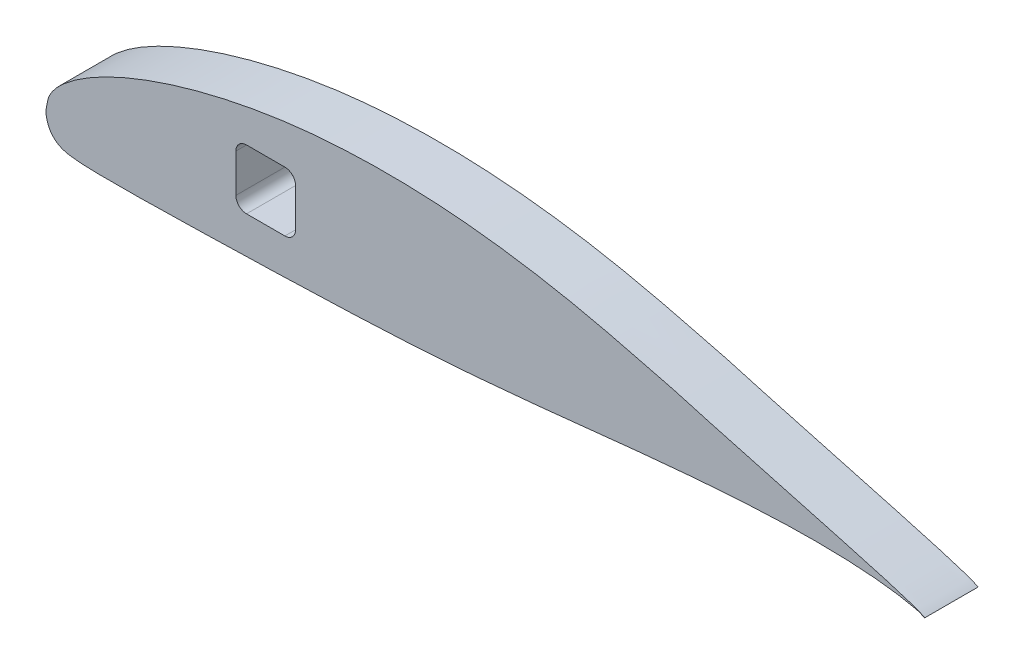
SolidWorks part; units mm, degrees
material "Wing Foam"
ref_plane "Front Plane" through (0, 0, 0) normal (0, 0, 1) x (1, 0, 0)
ref_plane "Top Plane" through (0, 0, 0) normal (0, 1, 0) x (1, 0, 0)
ref_plane "Right Plane" through (0, 0, 0) normal (1, 0, 0) x (0, 0, -1)
curve "Curve1"
  spline degree 3 poles (25.2073, 0.0831, 0) (25.4867, -0.0413, 0) (25.2065, 0.1018, 0) (25.0451, 0.1488, 0) (24.7905, 0.2354, 0) (24.512, 0.3191, 0) (24.1862, 0.415, 0) (23.8224, 0.5184, 0) (23.4192, 0.6311, 0) (22.9787, 0.7524, 0) (22.5024, 0.8828, 0) (21.992, 1.0218, 0) (21.4492, 1.1695, 0) (20.8759, 1.3256, 0) (20.2741, 1.4891, 0) (19.6466, 1.6619, 0) (18.9917, 1.8333, 0) (18.325, 2.0421, 0) (17.625, 2.2014, 0) (16.918, 2.3933, 0) (16.1932, 2.5703, 0) (15.4566, 2.7375, 0) (14.7104, 2.8879, 0) (13.9573, 3.0202, 0) (13.2001, 3.1321, 0) (12.4415, 3.2228, 0) (11.684, 3.2913, 0) (10.9305, 3.3367, 0) (10.1835, 3.3587, 0) (9.4457, 3.3585, 0) (8.7197, 3.336, 0) (8.0081, 3.2917, 0) (7.3132, 3.2267, 0) (6.6377, 3.1395, 0) (5.9841, 3.0331, 0) (5.3544, 2.9102, 0) (4.7508, 2.7729, 0) (4.1756, 2.6228, 0) (3.6307, 2.4616, 0) (3.118, 2.2911, 0) (2.6394, 2.1129, 0) (2.1964, 1.9285, 0) (1.7907, 1.7399, 0) (1.4236, 1.5487, 0) (1.0964, 1.3566, 0) (0.8101, 1.1655, 0) (0.5655, 0.9766, 0) (0.3618, 0.7902, 0) (0.2027, 0.6023, 0) (0.0715, 0.3961, 0) (0.0291, 0.1867, 0) (-0.0105, -0.0161, 0) (0.0146, -0.202, 0) (0.0835, -0.3893, 0) (0.1957, -0.5546, 0) (0.3573, -0.6861, 0) (0.5679, -0.7631, 0) (0.8154, -0.8005, 0) (1.1017, -0.8208, 0) (1.4284, -0.8311, 0) (1.795, -0.8378, 0) (2.2003, -0.8263, 0) (2.6429, -0.8333, 0) (3.1212, -0.8225, 0) (3.6335, -0.8137, 0) (4.1782, -0.8014, 0) (4.7531, -0.7878, 0) (5.3564, -0.7722, 0) (5.9859, -0.755, 0) (6.6394, -0.7358, 0) (7.3145, -0.7145, 0) (8.009, -0.6907, 0) (8.7203, -0.6638, 0) (9.446, -0.6335, 0) (10.1835, -0.5982, 0) (10.9302, -0.5555, 0) (11.6834, -0.5048, 0) (12.4406, -0.4465, 0) (13.199, -0.3808, 0) (13.956, -0.3084, 0) (14.7088, -0.2307, 0) (15.4548, -0.1506, 0) (16.1915, -0.0718, 0) (16.9163, 0.0037, 0) (17.6266, 0.0743, 0) (18.32, 0.1387, 0) (18.9939, 0.1957, 0) (19.646, 0.2444, 0) (20.274, 0.2839, 0) (20.8758, 0.3139, 0) (21.4491, 0.3334, 0) (21.9919, 0.3444, 0) (22.5024, 0.3431, 0) (22.9788, 0.3338, 0) (23.4193, 0.3149, 0) (23.8226, 0.2877, 0) (24.1865, 0.2533, 0) (24.5121, 0.2115, 0) (24.791, 0.1687, 0) (25.0447, 0.1113, 0) (25.2073, 0.0831, 0) (25.4867, -0.0413, 0) (25.2065, 0.1018, 0) knots -0.011667 -0.007006 -0.003134 0 0.003263 0.007251 0.012052 0.017662 0.024068 0.03125 0.039185 0.047848 0.057211 0.067242 0.077909 0.089174 0.100999 0.113341 0.126157 0.139462 0.153011 0.166928 0.181082 0.195404 0.209838 0.224333 0.238842 0.253325 0.26774 0.282049 0.296213 0.310196 0.323962 0.337476 0.350702 0.363611 0.376164 0.388326 0.400059 0.411327 0.422098 0.432339 0.44202 0.451113 0.459592 0.467435 0.474622 0.48114 0.486983 0.492171 0.496782 0.50097 0.505872 0.508789 0.51267 0.516326 0.52007 0.52388 0.527961 0.532642 0.538069 0.544264 0.551215 0.5589 0.567291 0.576362 0.58608 0.596409 0.607315 0.618758 0.630699 0.643095 0.655904 0.669079 0.682577 0.696348 0.710348 0.724529 0.738844 0.753243 0.767678 0.782097 0.796449 0.810678 0.824729 0.838548 0.852084 0.865288 0.878112 0.890511 0.902443 0.913866 0.924742 0.935036 0.944714 0.953747 0.962106 0.969765 0.976703 0.982899 0.988333 0.992994 0.996866 1 1.003263 1.007251 1.012052 periodic
sketch "Sketch4" plane through (0, 0, 0) normal (0, 0, 1) x (1, 0, 0)
  line L0 (292.1, 79.5958) -> (292.1, -43.6108) construction
  line L1 (292.1, 36.0891) -> (292.1, 1.334)
  line L2 (113.919, 33.5909) -> (95.631, 33.5909)
  line L3 (118.999, 28.5109) -> (118.999, 10.2229)
  line L4 (90.551, 28.5109) -> (90.551, 10.2229)
  line L5 (113.919, 5.1429) -> (95.631, 5.1429)
  line L6 (104.775, 51.0135) -> (104.775, -12.2796) construction
  arc A0 (118.999, 10.2229) -> (113.919, 5.1429) centre (113.919, 10.2229) cw
  arc A1 (90.551, 10.2229) -> (95.631, 5.1429) centre (95.631, 10.2229) ccw
  arc A2 (95.631, 33.5909) -> (90.551, 28.5109) centre (95.631, 28.5109) ccw
  arc A3 (118.999, 28.5109) -> (113.919, 33.5909) centre (113.919, 28.5109) ccw
  spline S1 degree 3 poles (415.9211, 1.3711) (420.5305, -0.682) (415.908, 1.6802) (413.2438, 2.4545) (409.0433, 3.884) (404.4481, 5.2647) (399.073, 6.8467) (393.0699, 8.5538) (386.4165, 10.4126) (379.1493, 12.4152) (371.2904, 14.5663) (362.8676, 16.8601) (353.9113, 19.2971) (344.4532, 21.873) (334.5234, 24.5699) (324.1693, 27.4216) (313.3627, 30.2499) (302.3629, 33.6946) (290.8121, 36.3225) (279.1478, 39.4898) (267.187, 42.4092) (255.0347, 45.1684) (242.7212, 47.6502) (230.2962, 49.8339) (217.8019, 51.68) (205.284, 53.1757) (192.7863, 54.3071) (180.3525, 55.0552) (168.027, 55.419) (155.8537, 55.4157) (143.8748, 55.0432) (132.1329, 54.3129) (120.6671, 53.2411) (109.5226, 51.8022) (98.7372, 50.0463) (88.3471, 48.019) (78.3889, 45.7523) (68.8976, 43.2761) (59.9068, 40.617) (51.4478, 37.8028) (43.5499, 34.862) (36.2413, 31.8209) (29.5472, 28.7079) (23.49, 25.5532) (18.0912, 22.3841) (13.3659, 19.2305) (9.3303, 16.1138) (5.9699, 13.039) (3.3452, 9.9386) (1.1802, 6.5357) (0.4796, 3.0799) (-0.1731, -0.2662) (0.2403, -3.3329) (1.3782, -6.4238) (3.2292, -9.1502) (5.896, -11.3207) (9.3708, -12.5914) (13.4534, -13.2083) (18.1779, -13.5437) (23.5691, -13.7123) (29.6183, -13.8232) (36.3042, -13.6335) (43.6074, -13.7495) (51.4991, -13.5705) (59.9532, -13.4254) (68.9395, -13.2237) (78.4265, -12.9982) (88.3809, -12.7417) (98.7674, -12.457) (109.5495, -12.1405) (120.6893, -11.7888) (132.1478, -11.3961) (143.8845, -10.9535) (155.8583, -10.4528) (168.0272, -9.87) (180.3479, -9.1658) (192.7765, -8.329) (205.27, -7.3671) (217.7837, -6.2836) (230.2734, -5.0881) (242.6944, -3.8057) (255.0037, -2.4847) (267.1595, -1.1839) (279.1189, 0.0609) (290.8394, 1.2255) (302.2794, 2.2893) (313.399, 3.2292) (324.1588, 4.0332) (334.5214, 4.6846) (344.4499, 5.1792) (353.9095, 5.5015) (362.8665, 5.6826) (371.2899, 5.6614) (379.15, 5.5073) (386.418, 5.1955) (393.0723, 4.7466) (399.0768, 4.1795) (404.4505, 3.49) (409.0513, 2.784) (413.237, 1.837) (415.9211, 1.3711) (420.5305, -0.682) (415.908, 1.6802) knots -0.011667 -0.007006 -0.003134 0 0.003263 0.007251 0.012052 0.017662 0.024068 0.03125 0.039185 0.047848 0.057211 0.067242 0.077909 0.089174 0.100999 0.113341 0.126157 0.139462 0.153011 0.166928 0.181082 0.195404 0.209838 0.224333 0.238842 0.253325 0.26774 0.282049 0.296213 0.310196 0.323962 0.337476 0.350702 0.363611 0.376164 0.388326 0.400059 0.411327 0.422098 0.432339 0.44202 0.451113 0.459592 0.467435 0.474622 0.48114 0.486983 0.492171 0.496782 0.50097 0.505872 0.508789 0.51267 0.516326 0.52007 0.52388 0.527961 0.532642 0.538069 0.544264 0.551215 0.5589 0.567291 0.576362 0.58608 0.596409 0.607315 0.618758 0.630699 0.643095 0.655904 0.669079 0.682577 0.696348 0.710348 0.724529 0.738844 0.753243 0.767678 0.782097 0.796449 0.810678 0.824729 0.838548 0.852084 0.865288 0.878112 0.890511 0.902443 0.913866 0.924742 0.935036 0.944714 0.953747 0.962106 0.969765 0.976703 0.982899 0.988333 0.992994 0.996866 1 1.003263 1.007251 1.012052 only from (419.1, 0) to (419.1, 0)
  point P14 (90.551, 5.1429)
  point P17 (90.551, 33.5909)
  point P20 (118.999, 33.5909)
  point P21 (104.775, 19.3669)
  point P29 (104.775, 33.5909)
  point P30 (104.775, 5.1429)
  point P31 (118.999, 19.3669)
  point P32 (90.551, 19.3669)
  dimension "D5" = 5.08
  dimension "D1" = 419.1
  dimension "D2" = 127
  dimension "D3" = 28.448
  dimension "D4" = 28.448
  dimension "D6" = 104.775
extrude "Boss-Extrude2" add sketch "Sketch4" along normal blind 25.4 contours L1 S1 | A3 L3 A0 L5 A1 L4 A2 L2
equation "\"AR\"= 7.5"
equation "\"Chord\"= 16.5"
equation "\"D1@Sketch4\"=\"Chord\""
equation "\"D1@Boss-Extrude2\"=1IN"
equation "\"D6@Sketch4\"=\"Chord\"/4"
